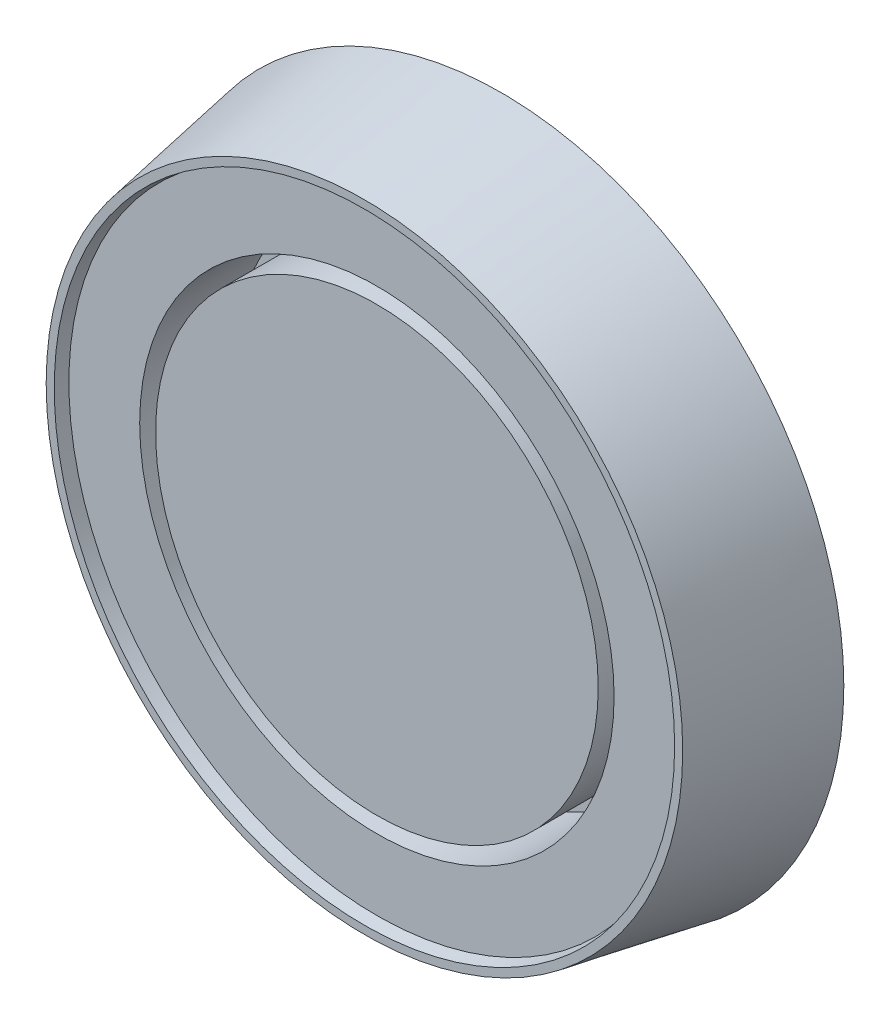
SolidWorks part; units mm, degrees
ref_plane "Front Plane" through (0, 0, 0) normal (0, 0, 1) x (1, 0, 0)
ref_plane "Top Plane" through (0, 0, 0) normal (0, 1, 0) x (1, 0, 0)
ref_plane "Right Plane" through (0, 0, 0) normal (1, 0, 0) x (0, 0, -1)
sketch "Sketch1" plane through (0, 0, 0) normal (0, 0, 1) x (1, 0, 0)
  circle A0 centre (0, 0) radius 55
  dimension "D1" = 110
extrude "Boss-Extrude1" add sketch "Sketch1" along normal blind 20 draft 10
sketch "Sketch2" plane through (0, 0, 20) normal (0, 0, 1) x (1, 0, 0)
  circle A0 centre (0, 0) radius 38.1
  circle A1 centre (0, 0) radius 35.55
  dimension "D1" = 76.2
  dimension "D2" = 71.1
extrude "Cut-Extrude1" cut sketch "Sketch2" against normal offset from surface (15 mm away) 5 up to face at (55, 0, 0)
sketch "Sketch3" plane through (0, 0, 20) normal (0, 0, 1) x (1, 0, 0)
  circle A0 centre (0, 0) radius 51.4735 construction
  circle A1 centre (0, 0) radius 51.4735
  circle A2 centre (0, 0) radius 49.4735
  dimension "D1" = 2
extrude "Boss-Extrude2" add sketch "Sketch3" along normal blind 2 draft 10
